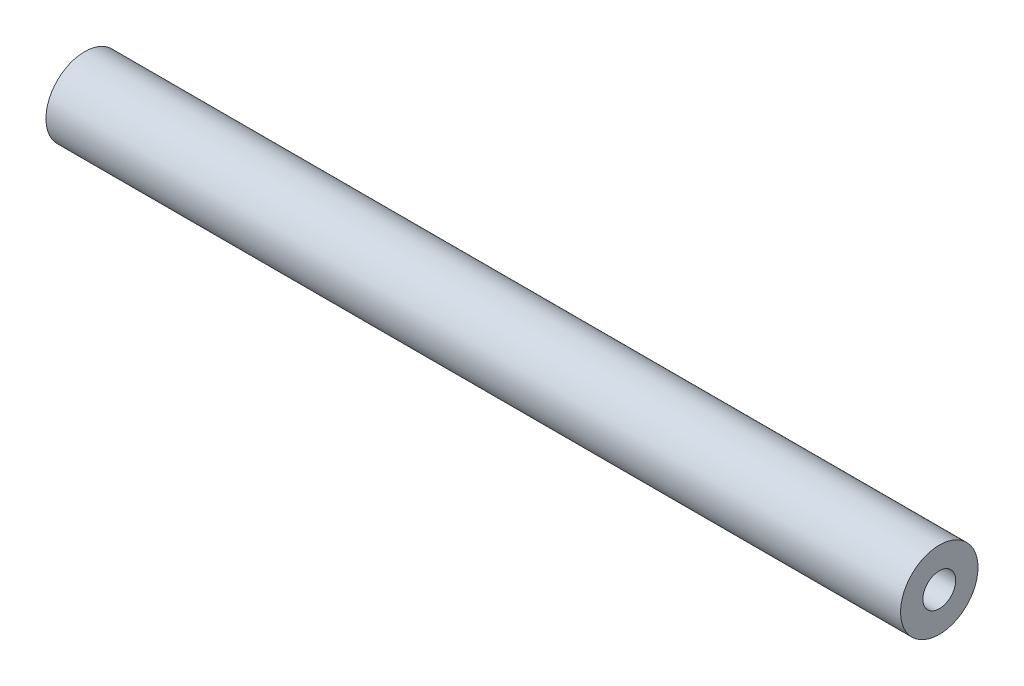
SolidWorks part; units mm, degrees
material "6061-T6 (SS)"
ref_plane "Front Plane" through (0, 0, 0) normal (0, 0, 1) x (1, 0, 0)
ref_plane "Top Plane" through (0, 0, 0) normal (0, 1, 0) x (1, 0, 0)
ref_plane "Right Plane" through (0, 0, 0) normal (1, 0, 0) x (0, 0, -1)
sketch "Sketch1" plane through (0, 0, 0) normal (1, 0, 0) x (0, 0, -1)
  circle A0 centre (0, 0) radius 4.7625
  dimension "D1" = 9.525
extrude "Boss-Extrude1" add sketch "Sketch1" along normal blind 105.156
hole_wizard "#10-32 Tapped Hole1" positions "Sketch5" profile "Sketch4" tap size "#10-32" standard "ANSI Inch" end condition through all
sketch "Sketch5" plane through (105.156, 0, 0) normal (1, 0, 0) x (0, 0, -1)
  point P0 (0, 0)
sketch "Sketch4" plane through (105.156, 0, 0) normal (0, 1, 0) x (0, 0, -1)
  line L0 (0, 0) -> (0, 105.156)
  line L1 (0, 105.156) -> (2.0193, 105.156)
  line L2 (2.0193, 105.156) -> (2.0193, 0)
  line L5 (2.0193, 0) -> (0, 0)
  line L11 (0, -6.35) -> (0, 107.95) construction
  dimension "Thru Tap Drill Dia." = 4.0386
  dimension "Thru Tap Drill Depth" = 105.156
cosmetic thread "Hole Thread1" parameters "D2"=4.826
